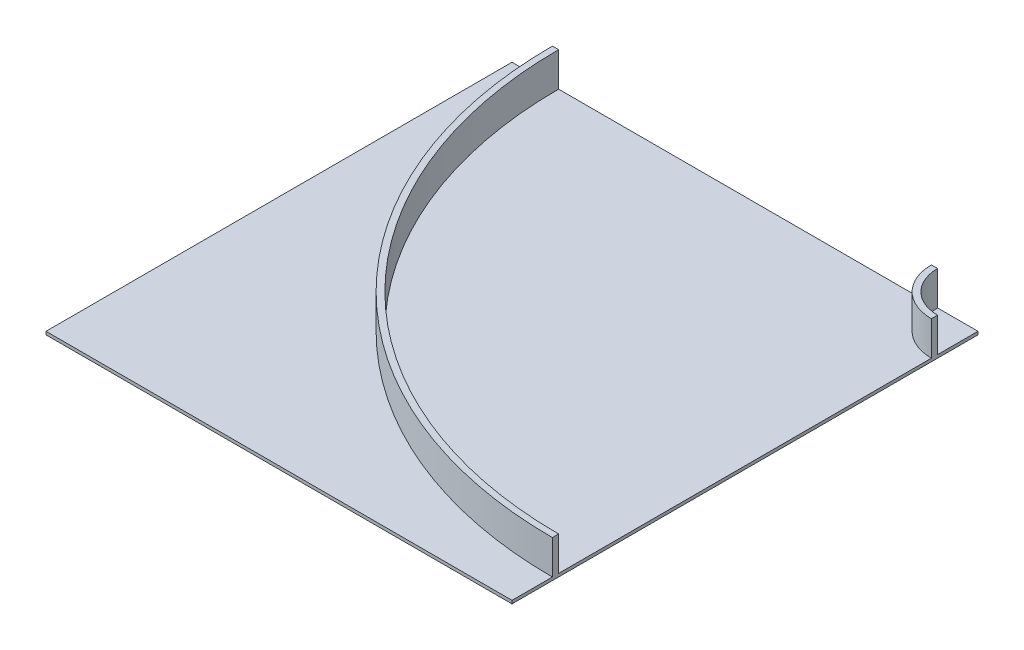
SolidWorks part; units mm, degrees
ref_plane "Front Plane" through (0, 0, 0) normal (0, 0, 1) x (1, 0, 0)
ref_plane "Top Plane" through (0, 0, 0) normal (0, 1, 0) x (1, 0, 0)
ref_plane "Right Plane" through (0, 0, 0) normal (1, 0, 0) x (0, 0, -1)
sketch "Sketch2" plane through (0, 0, 0) normal (0, 1, 0) x (1, 0, 0)
  line L1 (-750, 750) -> (750, 750)
  line L2 (-750, 750) -> (-750, -750)
  line L3 (-750, -750) -> (750, -750)
  line L4 (750, 750) -> (750, -750)
  line L5 (-750, 750) -> (750, -750) construction
  line L6 (-750, -750) -> (750, 750) construction
  point P0 (0, 0)
  dimension "D1" = 1500
  dimension "D2" = 1500
extrude "Boss-Extrude1" add sketch "Sketch2" along normal blind 10
sketch "Sketch3" plane through (0, 10, 0) normal (0, 1, 0) x (1, 0, 0)
  line L0 (620, 750) -> (620, -750) construction
  line L1 (750, 750) -> (-750, 750) construction
  line L2 (-750, -750) -> (750, -750) construction
  line L3 (600, 750) -> (600, -750) construction
  line L4 (750, -750) -> (750, 750) construction
  line L5 (-750, -600) -> (750, -600) construction
  line L6 (-750, 750) -> (-750, -750) construction
  line L7 (-750, -620) -> (750, -620) construction
  line L8 (-750, 0) -> (750, 0) construction
  line L9 (0, 750) -> (0, -750) construction
  line L10 (-750, 620) -> (750, 620) construction
  line L11 (-750, 600) -> (750, 600) construction
  line L12 (-620, 750) -> (-620, -750) construction
  line L13 (-600, 750) -> (-600, -750) construction
  circle A0 centre (750, 750) radius 150
  circle A1 centre (750, 750) radius 1350
  circle A2 centre (750, 750) radius 130
  circle A3 centre (750, 750) radius 1370
  line M3 (750, -750) -> (750, 750)
  line M4 (750, 750) -> (-750, 750)
  dimension "D6" = 150
  dimension "D5" = 20
  dimension "D7" = 20
  dimension "D8" = 150
extrude "Boss-Extrude2" add sketch "Sketch3" along normal blind 110 contours A3 A1 M4 M3 | A2 A0 M4 M3
equation "\"CellSize\"=1500"
equation "\"D1@Sketch2\"=\"CellSize\""
equation "\"D2@Sketch2\"=\"CellSize\""
equation "\"TrackWidth\"= 1200"
equation "\"C\"=342.079"
equation "\"WallWidth\"=20"
equation "\"D6@Sketch3\"=\"EdgeWidth\""
equation "\"D5@Sketch3\"=\"WallWidth\""
equation "\"D7@Sketch3\"=\"WallWidth\""
equation "\"EdgeWidth\"= ( \"CellSize\" - \"TrackWidth\" ) / 2"
equation "\"D8@Sketch3\"=\"EdgeWidth\""
